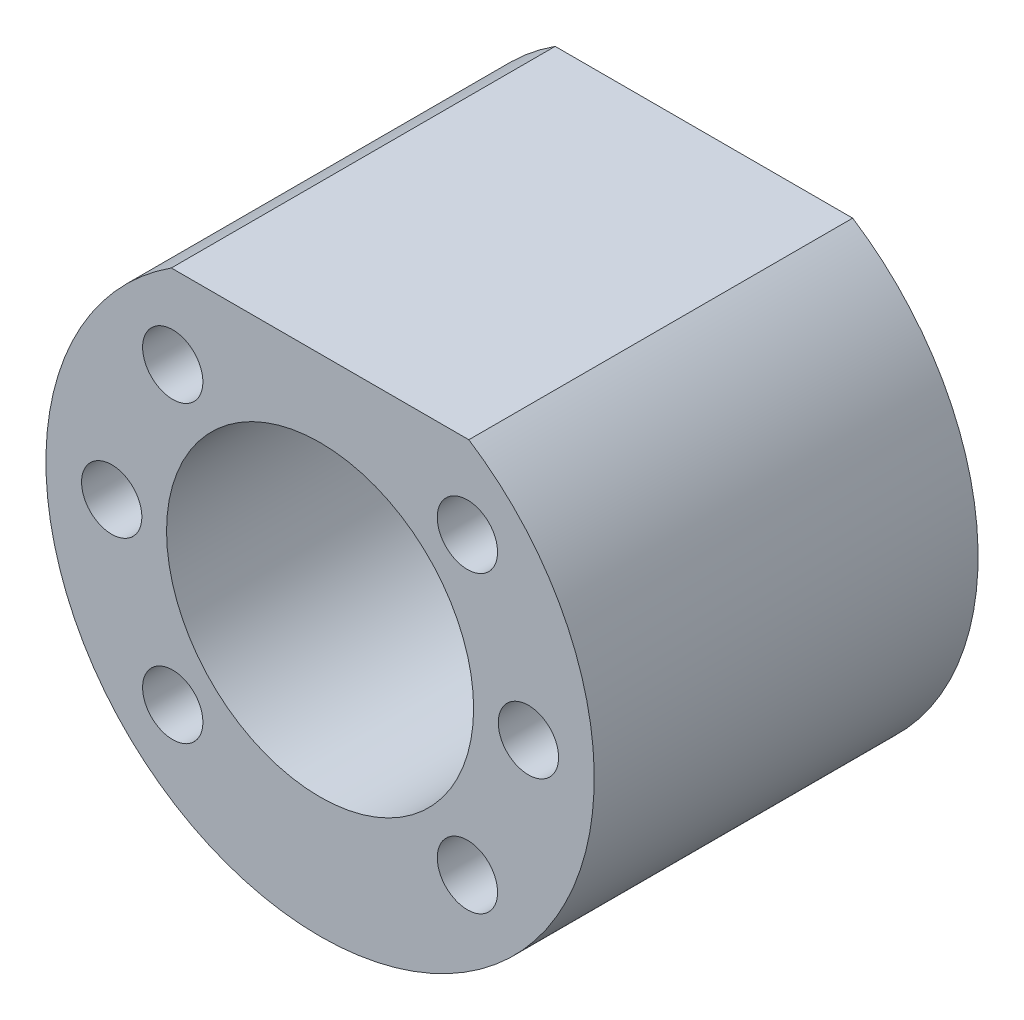
SolidWorks part; units mm, degrees
ref_plane "Front Plane" through (0, 0, 0) normal (0, 0, 1) x (1, 0, 0)
ref_plane "Top Plane" through (0, 0, 0) normal (0, 1, 0) x (1, 0, 0)
ref_plane "Right Plane" through (0, 0, 0) normal (1, 0, 0) x (0, 0, -1)
sketch "Sketch1" plane through (0, 0, 0) normal (0, 0, 1) x (1, 0, 0)
  circle A0 centre (0, 0) radius 25
  circle A1 centre (0, 0) radius 14
  dimension "D1" = 28
extrude "Boss-Extrude1" add sketch "Sketch1" along normal blind 35
sketch "Sketch2" plane through (0, 0, 35) normal (0, 0, 1) x (1, 0, 0)
  line L1 (-53.6905, 36.4122) -> (45.9125, 36.4122)
  line L2 (-53.6905, 36.4122) -> (-53.6905, 21)
  line L3 (-53.6905, 21) -> (45.9125, 21)
  line L4 (45.9125, 36.4122) -> (45.9125, 21)
  circle A0 centre (0, 0) radius 14 construction
  dimension "D1" = 21
extrude "Cut-Extrude1" cut sketch "Sketch2" against normal up to next
sketch "Sketch3" plane through (0, 0, 35) normal (0, 0, 1) x (1, 0, 0)
  line L0 (0, 0) -> (0, 36.9058) construction
  line L1 (0, 0) -> (-21.7429, 21.7429) construction
  line L2 (0, 0) -> (-32.9044, 0) construction
  line L3 (0, 0) -> (-23.9094, -23.9094) construction
  circle A0 centre (-13.435, 13.435) radius 2.75
  circle A1 centre (-19, 0) radius 2.75
  circle A2 centre (-13.435, -13.435) radius 2.75
  dimension "D3" = 5.5
  dimension "D4" = 5.5
  dimension "D5" = 5.5
  dimension "D1" = 45
  dimension "D2" = 45
  dimension "D6" = 19
  dimension "D7" = 19
  dimension "D8" = 19
extrude "Cut-Extrude2" cut sketch "Sketch3" against normal blind 16
mirror "Mirror1" about plane through (0, 0, 0) normal (1, 0, 0) of "Cut-Extrude2"
